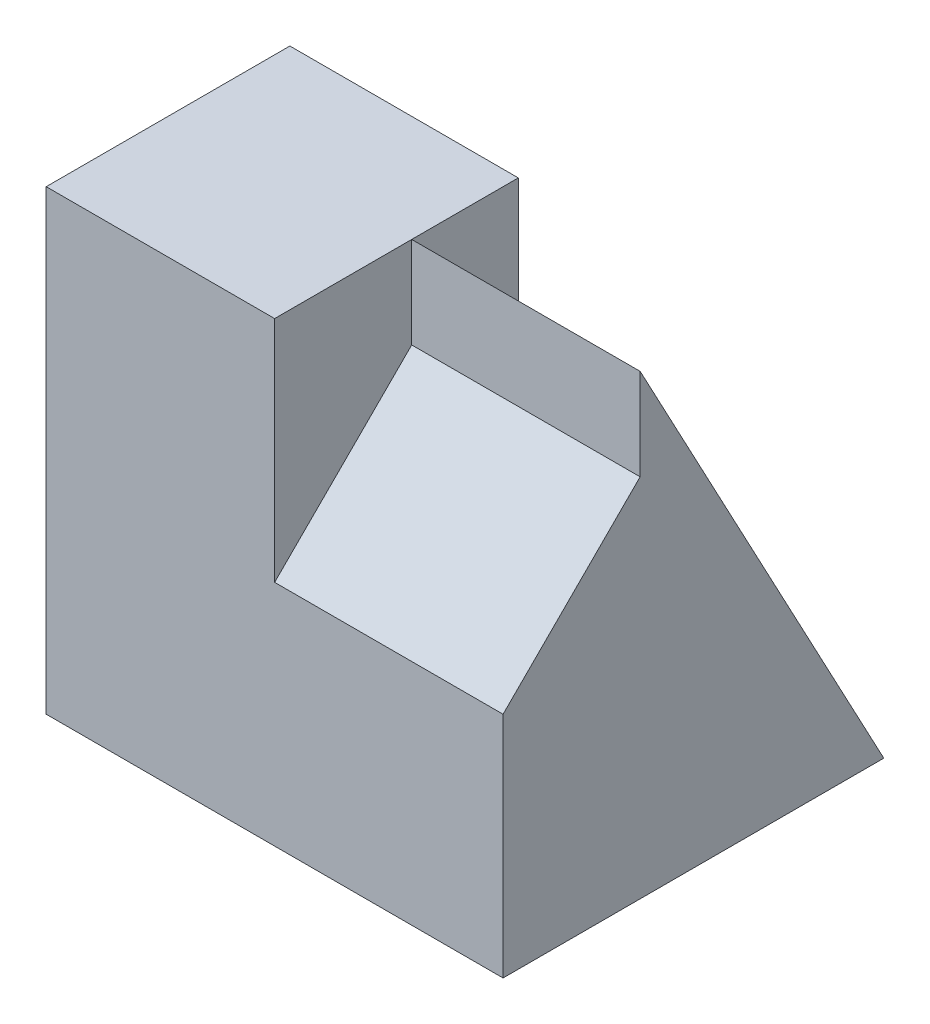
SolidWorks part; units mm, degrees
ref_plane "Front Plane" through (0, 0, 0) normal (0, 0, 1) x (1, 0, 0)
ref_plane "Top Plane" through (0, 0, 0) normal (0, 1, 0) x (1, 0, 0)
ref_plane "Right Plane" through (0, 0, 0) normal (1, 0, 0) x (0, 0, -1)
sketch "Sketch1" plane through (0, 0, 0) normal (1, 0, 0) x (0, 0, -1)
  line L0 (0, 0) -> (0, 3)
  line L1 (0, 3) -> (1.8, 4.8)
  line L2 (1.8, 4.8) -> (1.8, 6)
  line L3 (1.8, 6) -> (5, 0)
  line L4 (5, 0) -> (0, 0)
  dimension "D1" = 5
  dimension "D2" = 3
  dimension "D3" = 1.8
  dimension "D4" = 1.8
  dimension "D5" = 1.2
extrude "Boss-Extrude1" add sketch "Sketch1" along normal blind 3
sketch "Sketch2" plane through (0, 0, 0) normal (-1, 0, 0) x (0, 0, 1)
  line L0 (0, 0) -> (-5, 0) construction
  line L1 (0, 6) -> (-3.2, 6)
  line L2 (0, 6) -> (0, 0)
  line L3 (0, 0) -> (-3.2, 0)
  line L4 (-3.2, 6) -> (-3.2, 0)
  dimension "D1" = 6
  dimension "D2" = 3.2
extrude "Boss-Extrude2" add sketch "Sketch2" along normal blind 3
sketch "Sketch3" plane through (0, 0, 0) normal (-1, 0, 0) x (0, 0, 1)
  line L0 (-5, 0) -> (-3.2, 0)
  line L1 (-3.2, 0) -> (-3.2, 3.375)
  line L2 (-3.2, 3.375) -> (-5, 0)
extrude "Boss-Extrude3" add sketch "Sketch3" along normal blind 3
